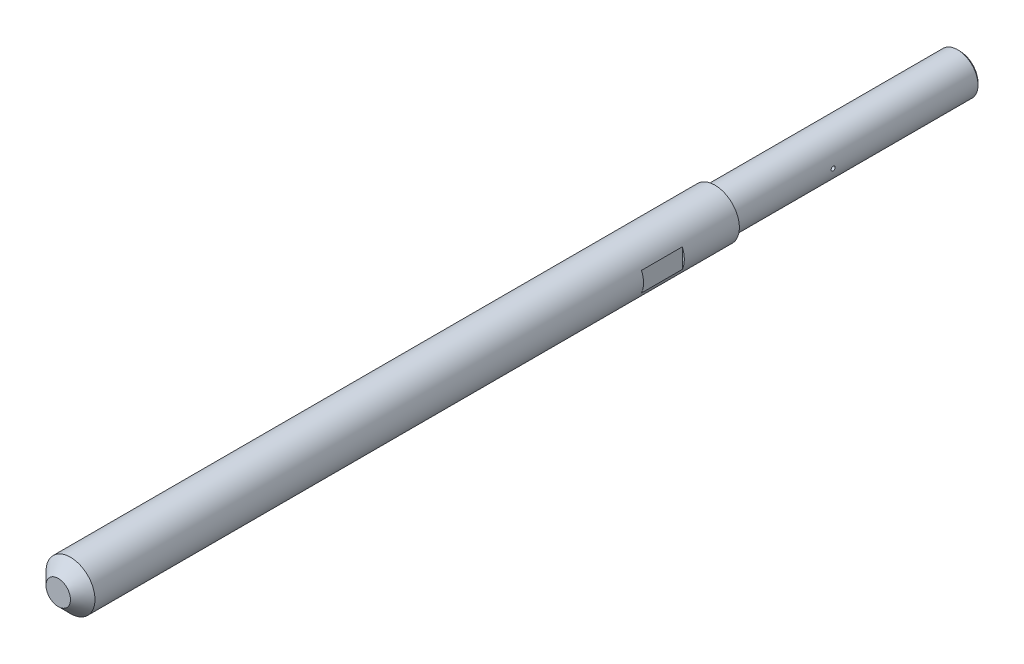
SolidWorks part; units mm, degrees
ref_plane "Front Plane" through (0, 0, 0) normal (0, 0, 1) x (1, 0, 0)
ref_plane "Top Plane" through (0, 0, 0) normal (0, 1, 0) x (1, 0, 0)
ref_plane "Right Plane" through (0, 0, 0) normal (1, 0, 0) x (0, 0, -1)
other "Center of Mass"
sketch "Sketch1" plane through (0, 0, 0) normal (0, 0, 1) x (1, 0, 0)
  circle A0 centre (0, 0) radius 5
  dimension "D1" = 10
extrude "Boss-Extrude1" add sketch "Sketch1" along normal blind 60
sketch "Sketch2" plane through (0, 0, 60) normal (0, 0, 1) x (1, 0, 0)
  circle A0 centre (0, 0) radius 6
  dimension "D1" = 12
extrude "Boss-Extrude2" add sketch "Sketch2" along normal blind 161
ref_plane "Plane1" through (5.5, 0, 0) normal (1, 0, 0) x (0, 0, -1)
sketch "Sketch3" plane through (5.5, 0, 0) normal (1, 0, 0) x (0, 0, -1)
  line L0 (0, -5) -> (0, 5) construction
  circle A0 centre (-36, 0) radius 0.5
  dimension "D1" = 1
  dimension "D2" = 36
extrude "Cut-Extrude1" cut sketch "Sketch3" against normal through all both and the other way through all
sketch "Sketch4" plane through (5.5, 0, 0) normal (1, 0, 0) x (0, 0, -1)
  line L0 (0, -5) -> (0, 5) construction
  line L1 (-83.5, 2.4681) -> (-73.5, 2.4681)
  line L2 (-83.5, 2.4681) -> (-83.5, -2.4681)
  line L3 (-83.5, -2.4681) -> (-73.5, -2.4681)
  line L4 (-73.5, 2.4681) -> (-73.5, -2.4681)
  line L5 (-83.5, 2.4681) -> (-73.5, -2.4681) construction
  line L6 (-83.5, -2.4681) -> (-73.5, 2.4681) construction
  point P0 (-78.5, 0)
  dimension "D1" = 83.5
  dimension "D2" = 10
extrude "Cut-Extrude2" cut sketch "Sketch4" along normal through all
hole_wizard "M5 Tapped Hole1" positions "Sketch5" profile "Sketch6" tap size "M5" standard "ISO"
sketch "Sketch5" plane through (0, 0, 0) normal (0, 0, -1) x (-1, 0, 0)
  point P0 (0, 0)
sketch "Sketch6" plane through (0, 0, 0) normal (1, 0, 0) x (0, 1, 0)
  line L0 (0, 0) -> (0, 11.2618)
  line L1 (0, 11.2618) -> (2.1, 10)
  line L2 (2.1, 10) -> (2.1, 0)
  line L5 (2.1, 0) -> (0, 0)
  line L10 (0, 11.2618) -> (-2.1, 10) construction
  line L11 (0, -6.35) -> (0, 107.95) construction
  dimension "Tap Drill Dia." = 4.2
  dimension "Tap Drill Depth" = 10
  dimension "Drill Angle" = 118
cosmetic thread "Hole Thread1" parameters "D1"=10, "D2"=5
chamfer "Chamfer1" distance 3 angle 45 1 edges at (6, 0, 221)
chamfer "Chamfer2" distance 0.5 angle 45 1 edges at (5, 0, 0)
ref_plane "Plane4" through (0, -5.5, 0) normal (0, 1, 0) x (1, 0, 0)
sketch "Sketch8" plane through (0, -5.5, 0) normal (0, 1, 0) x (1, 0, 0)
  line L0 (4.5, 0) -> (-4.5, 0) construction
  line L1 (1.9891, -95) -> (-3.0109, -95)
  line L2 (1.9891, -95) -> (1.9891, -65)
  line L3 (1.9891, -65) -> (-3.0109, -65)
  line L4 (-3.0109, -95) -> (-3.0109, -65)
  line L5 (1.9891, -95) -> (-3.0109, -65) construction
  line L6 (1.9891, -65) -> (-3.0109, -95) construction
  point P0 (-0.5109, -80)
  dimension "D1" = 30
  dimension "D2" = 65
  dimension "D3" = 5
extrude "Cut-Extrude3" cut sketch "Sketch8" against normal blind 161
